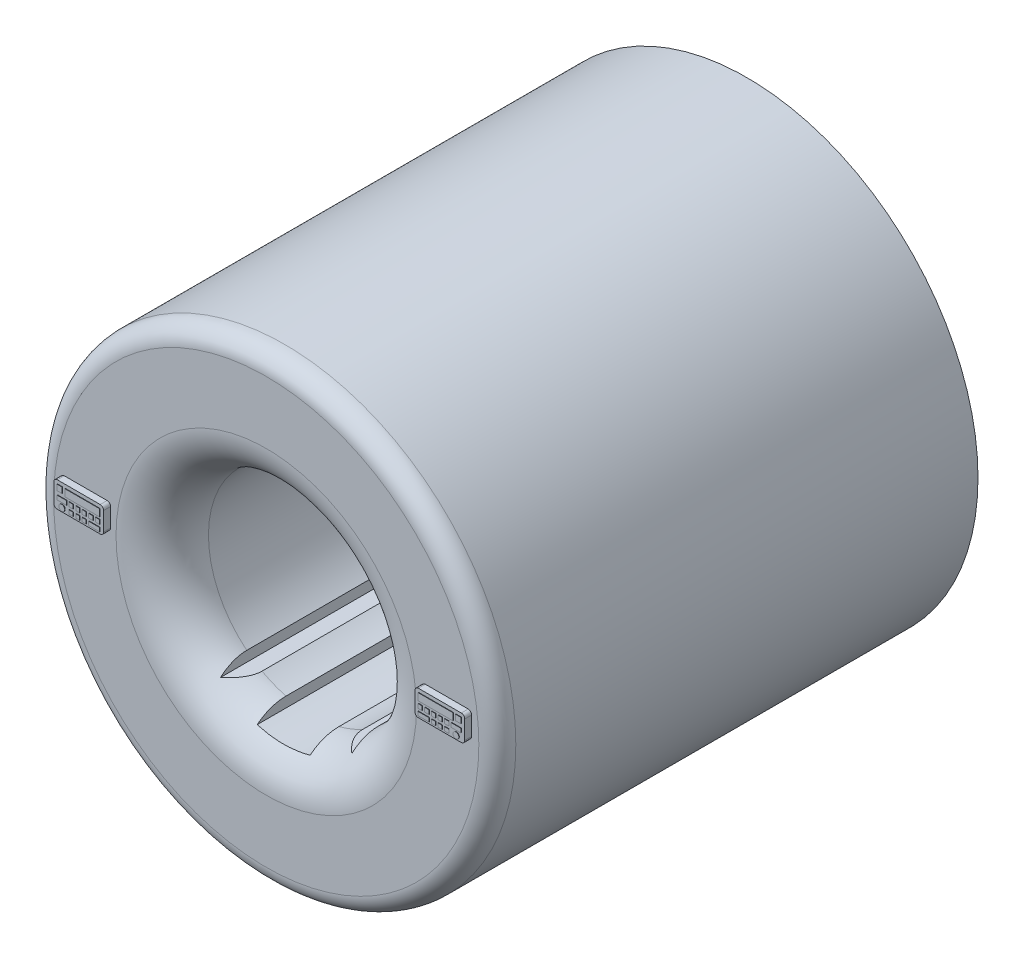
SolidWorks part; units mm, degrees
ref_plane "Front Plane" through (0, 0, 0) normal (0, 0, 1) x (1, 0, 0)
ref_plane "Top Plane" through (0, 0, 0) normal (0, 1, 0) x (1, 0, 0)
ref_plane "Right Plane" through (0, 0, 0) normal (1, 0, 0) x (0, 0, -1)
sketch "Sketch1" plane through (0, 0, 0) normal (0, 0, 1) x (1, 0, 0)
  circle A0 centre (0, 0) radius 100
  circle A1 centre (0, 0) radius 45
extrude "Boss-Extrude1" add sketch "Sketch1" along normal blind 200
fillet "Fillet1" radius 8 1 edges at (100, 0, 200)
fillet "Fillet2" radius 20 1 edges at (45, 0, 200)
sketch "Sketch2" plane through (0, 0, 0) normal (0, 0, -1) x (-1, 0, 0)
  line L0 (-28.4316, -34.8804) -> (28.4316, -34.8804)
  line L1 (-28.4316, -34.8804) -> (-28.4316, -39.3611)
  line L2 (-28.4316, -39.3611) -> (-11.4457, -39.3611)
  line L3 (-11.4457, -39.3611) -> (-11.4457, -48.0007)
  line L5 (11.4457, -39.3611) -> (11.4457, -48.0007)
  line L6 (28.4316, -39.3611) -> (11.4457, -39.3611)
  line L7 (28.4316, -34.8804) -> (28.4316, -39.3611)
  arc A1 (-11.4457, -48.0007) -> (11.4457, -48.0007) centre (0, -4.4806) ccw
extrude "Cut-Extrude1" cut sketch "Sketch2" against normal blind 200
sketch "Sketch3" plane through (0, 0, 200) normal (0, 0, 1) x (1, 0, 0)
  line L1 (67.3499, 0) -> (88.8941, 0)
  line L2 (67.3499, 0) -> (67.3499, 11.0573)
  line L3 (67.3499, 11.0573) -> (88.8941, 11.0573)
  line L4 (88.8941, 0) -> (88.8941, 11.0573)
  line L5 (-88.8941, 0) -> (-88.8941, 11.0573)
  line L6 (-67.3499, 11.0573) -> (-88.8941, 11.0573)
  line L7 (-67.3499, 0) -> (-67.3499, 11.0573)
  line L8 (-67.3499, 0) -> (-88.8941, 0)
extrude "Boss-Extrude2" add sketch "Sketch3" along normal blind 3
fillet "Fillet3" radius 1.5 8 edges at (-67.3499, 11.0573, 201.5) (-67.3499, 0, 201.5) (-88.8941, 11.0573, 201.5) (-88.8941, 0, 201.5) (67.3499, 0, 201.5) (88.8941, 0, 201.5) (67.3499, 11.0573, 201.5) (88.8941, 11.0573, 201.5)
sketch "Sketch4" plane through (0, 0, 203) normal (0, 0, 1) x (1, 0, 0)
  line L1 (68.8499, 9.5573) -> (83.9814, 9.5573)
  line L2 (68.8499, 9.5573) -> (68.8499, 6.4921)
  line L3 (68.8499, 6.4921) -> (83.9814, 6.4921)
  line L4 (83.9814, 9.5573) -> (83.9814, 6.4921)
  line L5 (85.0941, 9.5573) -> (87.3941, 9.5573)
  line L6 (85.0941, 9.5573) -> (85.0941, 7.1279)
  line L7 (85.0941, 7.1279) -> (87.3941, 7.1279)
  line L8 (87.3941, 9.5573) -> (87.3941, 7.1279)
  line L9 (68.8499, 5.4589) -> (70.669, 5.4589)
  line L10 (68.8499, 5.4589) -> (68.8499, 3.6707)
  line L11 (68.8499, 3.6707) -> (70.669, 3.6707)
  line L12 (70.669, 5.4589) -> (70.669, 3.6707)
  line L13 (71.7817, 5.4589) -> (73.6097, 5.4589)
  line L14 (71.7817, 5.4589) -> (71.7817, 3.6707)
  line L15 (71.7817, 3.6707) -> (73.6097, 3.6707)
  line L16 (73.6097, 5.4589) -> (73.6097, 3.6707)
  line L17 (74.7224, 5.4589) -> (76.4157, 5.4589)
  line L18 (74.7224, 5.4589) -> (74.7224, 3.6707)
  line L19 (74.7224, 3.6707) -> (76.4157, 3.6707)
  line L20 (76.4157, 5.4589) -> (76.4157, 3.6707)
  line L21 (77.5041, 5.4589) -> (79.2128, 5.4589)
  line L22 (77.5041, 5.4589) -> (77.5041, 3.6707)
  line L23 (77.5041, 3.6707) -> (79.2128, 3.6707)
  line L24 (79.2128, 5.4589) -> (79.2128, 3.6707)
  line L25 (80.3255, 5.4589) -> (82.1932, 5.4589)
  line L26 (80.3255, 5.4589) -> (80.3255, 3.6707)
  line L27 (80.3255, 3.6707) -> (82.1932, 3.6707)
  line L28 (82.1932, 5.4589) -> (82.1932, 3.6707)
  line L29 (83.1469, 5.4589) -> (87.3941, 5.4589)
  line L30 (83.1469, 5.4589) -> (83.1469, 3.6707)
  line L31 (83.1469, 3.6707) -> (87.3941, 3.6707)
  line L32 (87.3941, 5.4589) -> (87.3941, 3.6707)
  line L33 (68.8499, 2.5182) -> (73.6097, 2.5182)
  line L34 (68.8499, 2.5182) -> (68.8499, 0.889)
  line L35 (68.8499, 0.889) -> (73.6097, 0.889)
  line L36 (73.6097, 2.5182) -> (73.6097, 0.889)
  line L37 (74.7224, 2.5182) -> (76.4157, 2.5182)
  line L38 (74.7224, 2.5182) -> (74.7224, 0.889)
  line L39 (74.7224, 0.889) -> (76.4157, 0.889)
  line L40 (76.4157, 2.5182) -> (76.4157, 0.889)
  line L41 (77.5041, 2.5182) -> (79.2128, 2.5182)
  line L42 (77.5041, 2.5182) -> (77.5041, 0.889)
  line L43 (77.5041, 0.889) -> (79.2128, 0.889)
  line L44 (79.2128, 2.5182) -> (79.2128, 0.889)
  line L45 (80.3255, 2.5182) -> (82.1932, 2.5182)
  line L46 (80.3255, 2.5182) -> (80.3255, 0.889)
  line L47 (80.3255, 0.889) -> (82.1932, 0.889)
  line L48 (82.1932, 2.5182) -> (82.1932, 0.889)
  line L49 (-82.1932, 2.5182) -> (-82.1932, 0.889)
  line L50 (-80.3255, 0.889) -> (-82.1932, 0.889)
  line L51 (-80.3255, 2.5182) -> (-80.3255, 0.889)
  line L52 (-80.3255, 2.5182) -> (-82.1932, 2.5182)
  line L53 (-79.2128, 2.5182) -> (-79.2128, 0.889)
  line L54 (-77.5041, 0.889) -> (-79.2128, 0.889)
  line L55 (-77.5041, 2.5182) -> (-77.5041, 0.889)
  line L56 (-77.5041, 2.5182) -> (-79.2128, 2.5182)
  line L57 (-76.4157, 2.5182) -> (-76.4157, 0.889)
  line L58 (-74.7224, 0.889) -> (-76.4157, 0.889)
  line L59 (-74.7224, 2.5182) -> (-74.7224, 0.889)
  line L60 (-74.7224, 2.5182) -> (-76.4157, 2.5182)
  line L61 (-73.6097, 2.5182) -> (-73.6097, 0.889)
  line L62 (-68.8499, 0.889) -> (-73.6097, 0.889)
  line L63 (-68.8499, 2.5182) -> (-68.8499, 0.889)
  line L64 (-68.8499, 2.5182) -> (-73.6097, 2.5182)
  line L65 (-87.3941, 5.4589) -> (-87.3941, 3.6707)
  line L66 (-83.1469, 3.6707) -> (-87.3941, 3.6707)
  line L67 (-83.1469, 5.4589) -> (-83.1469, 3.6707)
  line L68 (-83.1469, 5.4589) -> (-87.3941, 5.4589)
  line L69 (-82.1932, 5.4589) -> (-82.1932, 3.6707)
  line L70 (-80.3255, 3.6707) -> (-82.1932, 3.6707)
  line L71 (-80.3255, 5.4589) -> (-80.3255, 3.6707)
  line L72 (-80.3255, 5.4589) -> (-82.1932, 5.4589)
  line L73 (-79.2128, 5.4589) -> (-79.2128, 3.6707)
  line L74 (-77.5041, 3.6707) -> (-79.2128, 3.6707)
  line L75 (-77.5041, 5.4589) -> (-77.5041, 3.6707)
  line L76 (-77.5041, 5.4589) -> (-79.2128, 5.4589)
  line L77 (-76.4157, 5.4589) -> (-76.4157, 3.6707)
  line L78 (-74.7224, 3.6707) -> (-76.4157, 3.6707)
  line L79 (-74.7224, 5.4589) -> (-74.7224, 3.6707)
  line L80 (-74.7224, 5.4589) -> (-76.4157, 5.4589)
  line L81 (-73.6097, 5.4589) -> (-73.6097, 3.6707)
  line L82 (-71.7817, 3.6707) -> (-73.6097, 3.6707)
  line L83 (-71.7817, 5.4589) -> (-71.7817, 3.6707)
  line L84 (-71.7817, 5.4589) -> (-73.6097, 5.4589)
  line L85 (-70.669, 5.4589) -> (-70.669, 3.6707)
  line L86 (-68.8499, 3.6707) -> (-70.669, 3.6707)
  line L87 (-68.8499, 5.4589) -> (-68.8499, 3.6707)
  line L88 (-68.8499, 5.4589) -> (-70.669, 5.4589)
  line L89 (-87.3941, 9.5573) -> (-87.3941, 7.1279)
  line L90 (-85.0941, 7.1279) -> (-87.3941, 7.1279)
  line L91 (-85.0941, 9.5573) -> (-85.0941, 7.1279)
  line L92 (-85.0941, 9.5573) -> (-87.3941, 9.5573)
  line L93 (-83.9814, 9.5573) -> (-83.9814, 6.4921)
  line L94 (-68.8499, 6.4921) -> (-83.9814, 6.4921)
  line L95 (-68.8499, 9.5573) -> (-68.8499, 6.4921)
  line L96 (-68.8499, 9.5573) -> (-83.9814, 9.5573)
  circle A0 centre (85.2705, 1.7036) radius 1.2891
  circle A1 centre (-85.2705, 1.7036) radius 1.2891
extrude "Boss-Extrude3" add sketch "Sketch4" along normal blind 0.2
sketch "Sketch5" plane through (0, 0, 0) normal (0, 0, -1) x (-1, 0, 0)
  line L0 (-28.4316, -34.8804) -> (-28.4316, -39.3611)
  line L1 (-28.4316, -39.3611) -> (-21.8107, -39.3611)
  line L2 (-11.4457, -43.5201) -> (-11.4457, -48.0007)
  line L3 (11.4457, -43.5201) -> (11.4457, -48.0007)
  line L4 (11.4457, -48.0007) -> (11.4457, -45.7604)
  line L5 (28.4316, -34.8804) -> (28.4316, -39.3611)
  line L6 (28.4316, -39.3611) -> (21.8107, -39.3611)
  circle A0 centre (0, 0) radius 100
  arc A1 (28.4316, -34.8804) -> (-28.4316, -34.8804) centre (0, 0) ccw
  arc A2 (28.4316, -34.8804) -> (-28.4316, -34.8804) centre (0, 0) ccw construction
  arc A3 (-11.4457, -48.0007) -> (11.4457, -48.0007) centre (0, 0) ccw
  arc A4 (-11.4457, -48.0007) -> (11.4457, -48.0007) centre (0, -4.4806) ccw construction
  arc A5 (11.4457, -43.5201) -> (21.8107, -39.3611) centre (0, 0) ccw
  arc A6 (11.4457, -43.5201) -> (21.8107, -39.3611) centre (0, 0) ccw construction
  arc A7 (-21.8107, -39.3611) -> (-11.4457, -43.5201) centre (0, 0) ccw
  arc A8 (-21.8107, -39.3611) -> (-11.4457, -43.5201) centre (0, 0) ccw construction
  circle M1 centre (0, 0) radius 100
  arc M2 (-11.4457, -43.5201) -> (-21.8107, -39.3611) centre (0, 0) cw
  line M3 (-21.8107, -39.3611) -> (-28.4316, -39.3611)
  line M4 (-28.4316, -39.3611) -> (-28.4316, -34.8804)
  arc M5 (-28.4316, -34.8804) -> (28.4316, -34.8804) centre (0, 0) cw
  line M6 (28.4316, -34.8804) -> (28.4316, -39.3611)
  line M7 (28.4316, -39.3611) -> (21.8107, -39.3611)
  arc M8 (21.8107, -39.3611) -> (11.4457, -43.5201) centre (0, 0) cw
  line M9 (11.4457, -43.5201) -> (11.4457, -48.0007)
  arc M10 (11.4457, -48.0007) -> (-11.4457, -48.0007) centre (0, -4.4806) cw
  line M11 (-11.4457, -48.0007) -> (-11.4457, -43.5201)
extrude "Boss-Extrude4" add sketch "Sketch5" along normal blind 8 contours L3 M1 M11 M2 M3 M4 M5 M6 M7 M8 M9 M10
scale "Scale1" scale about centroid uniform scaling yes scale factor 15.6
scale "Scale2" scale about centroid uniform scaling yes scale factor 0.5
